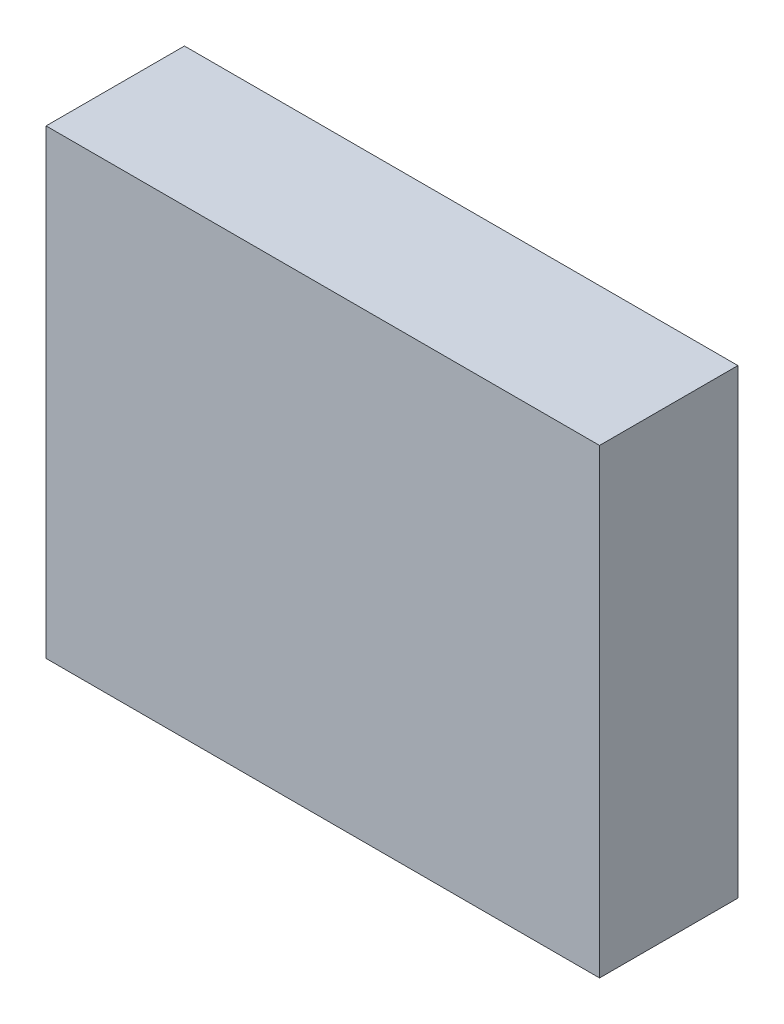
SolidWorks part; units mm, degrees
ref_plane "Front Plane" through (0, 0, 0) normal (0, 0, 1) x (1, 0, 0)
ref_plane "Top Plane" through (0, 0, 0) normal (0, 1, 0) x (1, 0, 0)
ref_plane "Right Plane" through (0, 0, 0) normal (1, 0, 0) x (0, 0, -1)
sketch "Sketch1" plane through (0, 0, 0) normal (0, 0, 1) x (1, 0, 0)
  line L1 (-6, -5) -> (6, -5)
  line L2 (-6, -5) -> (-6, 5)
  line L3 (-6, 5) -> (6, 5)
  line L4 (6, -5) -> (6, 5)
  line L5 (-6, -5) -> (6, 5) construction
  line L6 (-6, 5) -> (6, -5) construction
  point P0 (0, 0)
  dimension "D1" = 10
  dimension "D2" = 12
extrude "Boss-Extrude1" add sketch "Sketch1" along normal blind 3
